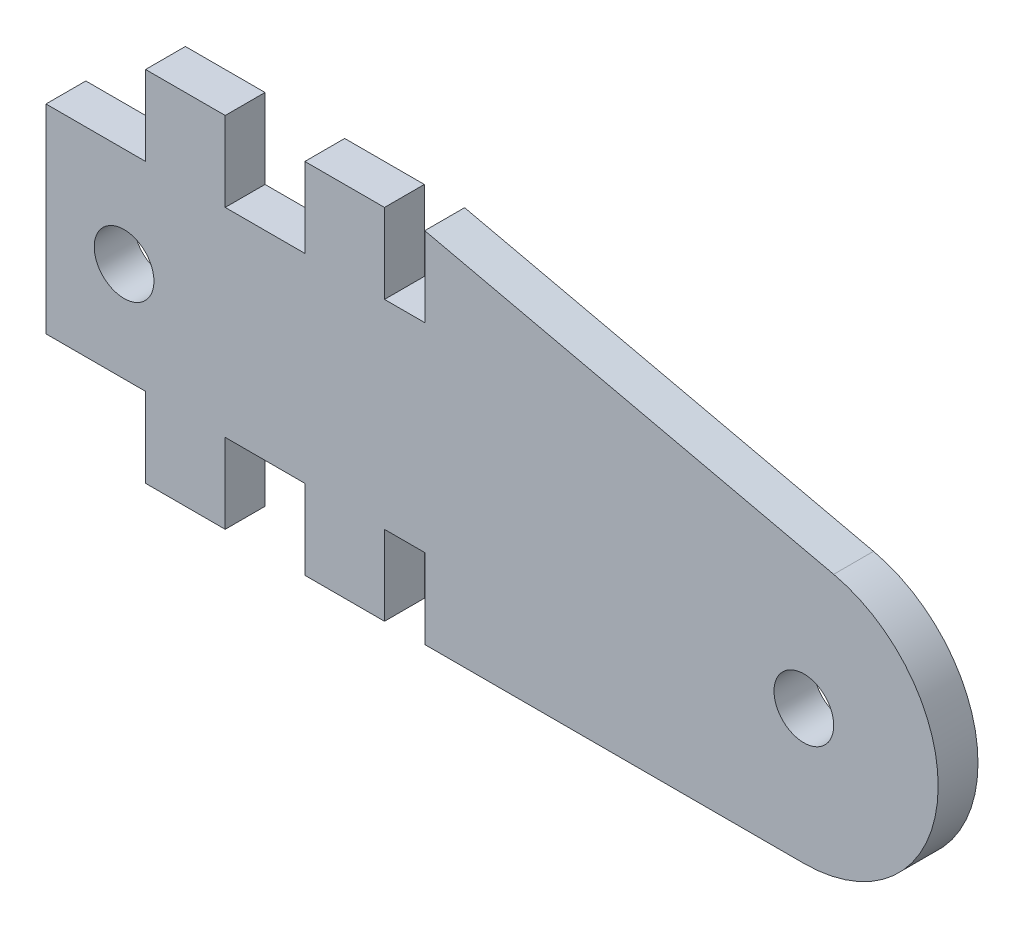
SolidWorks part; units mm, degrees
ref_plane "Front Plane" through (0, 0, 0) normal (0, 0, 1) x (1, 0, 0)
ref_plane "Top Plane" through (0, 0, 0) normal (0, 1, 0) x (1, 0, 0)
ref_plane "Right Plane" through (0, 0, 0) normal (1, 0, 0) x (0, 0, -1)
sketch "Sketch1" plane through (0, 0, 0) normal (0, 0, 1) x (1, 0, 0)
  line L0 (5, 0) -> (9, 0)
  line L1 (5, 4) -> (5, 0)
  line L2 (5, 14) -> (0, 14)
  line L3 (9, 4) -> (13, 4)
  line L4 (13, 4) -> (13, 0)
  line L5 (9, 0) -> (9, 4)
  line L6 (13, 0) -> (17, 0)
  line L7 (17, 0) -> (17, 4)
  line L8 (17, 4) -> (19.0216, 4)
  line L9 (0, 14) -> (0, 4)
  line L10 (19.0216, 4) -> (19.0216, 0)
  line L11 (17, 14) -> (19.0216, 14)
  line L12 (17, 18) -> (17, 14)
  line L13 (13, 18) -> (17, 18)
  line L14 (9, 18) -> (9, 14)
  line L15 (13, 14) -> (13, 18)
  line L16 (9, 14) -> (13, 14)
  line L17 (0, 4) -> (5, 4)
  line L18 (5, 14) -> (5, 18)
  line L19 (5, 18) -> (9, 18)
  line L20 (19.0216, 0) -> (38.0595, 0)
  line L21 (27.99, 0) -> (27.99, -6.4753) construction
  line L22 (19.0216, 14) -> (19.0216, 18)
  line L23 (19.0216, 18) -> (39.5576, 13.3222)
  line L27 (23.6391, 12.0249) -> (21.6695, 11.6776) construction
  line L32 (16.7455, 10.8093) -> (17.6137, 5.8853) construction
  line L33 (16.7455, 10.8093) -> (14.7759, 10.462) construction
  line L34 (14.7759, 10.462) -> (15.6441, 5.538) construction
  line L35 (15.6441, 5.538) -> (17.6137, 5.8853) construction
  line L36 (21.6695, 11.6776) -> (22.5378, 6.7535) construction
  line L37 (22.5378, 6.7535) -> (24.5074, 7.1008) construction
  line L38 (23.6391, 12.0249) -> (24.5074, 7.1008) construction
  arc A0 (38.0595, 0) -> (39.5576, 13.3222) centre (38.0595, 6.7453) ccw
  circle A1 centre (3.9205, 9) radius 1.5
  circle A2 centre (38.0595, 6.7453) radius 12.12 construction
  circle A4 centre (38.0595, 6.7453) radius 1.5
  dimension "D16" = 9
  dimension "D13" = 5.8853
  dimension "D1" = 3
  dimension "D2" = 6.7453
  dimension "D7" = 24.24
  dimension "D3" = 3.9205
  dimension "D4" = 14.7759
  dimension "D5" = 15.6441
  dimension "D6" = 16.7455
  dimension "D8" = 21.6695
  dimension "D9" = 9
  dimension "D10" = 18
  dimension "D11" = 19.0216
  dimension "D12" = 5.538
  dimension "ThumbLinkLengthMCP" = 18.99
extrude "Boss-Extrude1" add sketch "Sketch1" along normal blind 2
equation "\"ThumbLinkLengthMCP@Sketch1\"= \"HB@parametersSketch@prostheticParameters.SLDPRT\" * 0.211"
